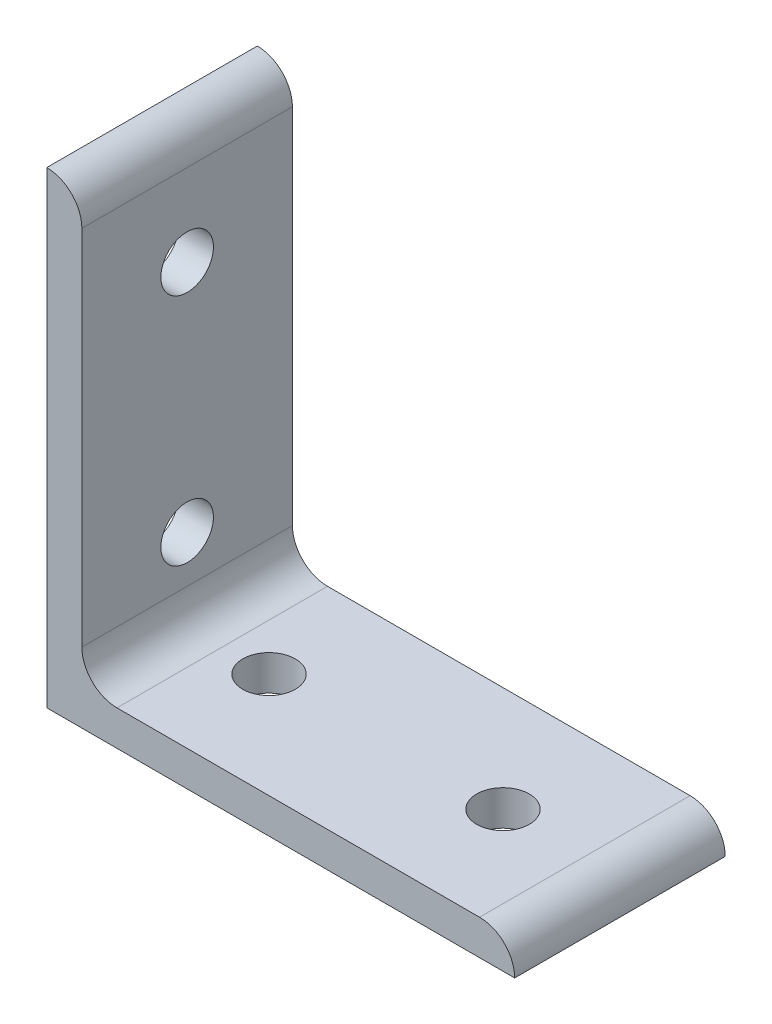
SolidWorks part; units mm, degrees
ref_plane "Front Plane" through (0, 0, 0) normal (0, 0, 1) x (1, 0, 0)
ref_plane "Top Plane" through (0, 0, 0) normal (0, 1, 0) x (1, 0, 0)
ref_plane "Right Plane" through (0, 0, 0) normal (1, 0, 0) x (0, 0, -1)
sketch "Sketch1" plane through (0, 0, 0) normal (0, 0, 1) x (1, 0, 0)
  line L0 (0, 0) -> (0, 80)
  line L1 (6, 74) -> (6, 80) construction
  line L2 (6, 74) -> (6, 12)
  line L3 (12, 6) -> (74, 6)
  line L4 (6, 80) -> (0, 80) construction
  line L5 (80, 0) -> (0, 0)
  line L6 (74, 6) -> (80, 6) construction
  line L7 (80, 6) -> (80, 0) construction
  arc A0 (6, 74) -> (0, 80) centre (0, 74) ccw
  arc A1 (80, 0) -> (74, 6) centre (74, 0) ccw
  arc A2 (6, 12) -> (12, 6) centre (12, 12) ccw
  point P10 (6, 77)
  dimension "E" = 6
  dimension "D" = 6
  dimension "C" = 80
  dimension "B" = 80
extrude "Boss-Extrude1" add sketch "Sketch1" along normal mid plane 36
sketch "Sketch2" plane through (0, 0, 0) normal (0, 1, 0) x (1, 0, 0)
  line L0 (0, 0) -> (20, 0) construction
  line L1 (20, 0) -> (60, 0) construction
  circle A0 centre (20, 0) radius 4.5
  circle A1 centre (60, 0) radius 4.5
extrude "Cut-Extrude1" cut sketch "Sketch2" along normal through all
sketch "Sketch3" plane through (0, 0, 0) normal (1, 0, 0) x (0, 0, -1)
  line L0 (0, 0) -> (0, 20) construction
  line L1 (0, 20) -> (0, 60) construction
  circle A0 centre (0, 20) radius 4.5
  circle A1 centre (0, 60) radius 4.5
  dimension "D1" = 20
  dimension "D2" = 40
extrude "Cut-Extrude2" cut sketch "Sketch3" along normal through all
equation "\"E@Sketch3\" = \"E@Sketch2\""
equation "\"D1@Sketch3\" = \"D1@Sketch2\""
equation "\"D2@Sketch3\" = \"D2@Sketch2\""
